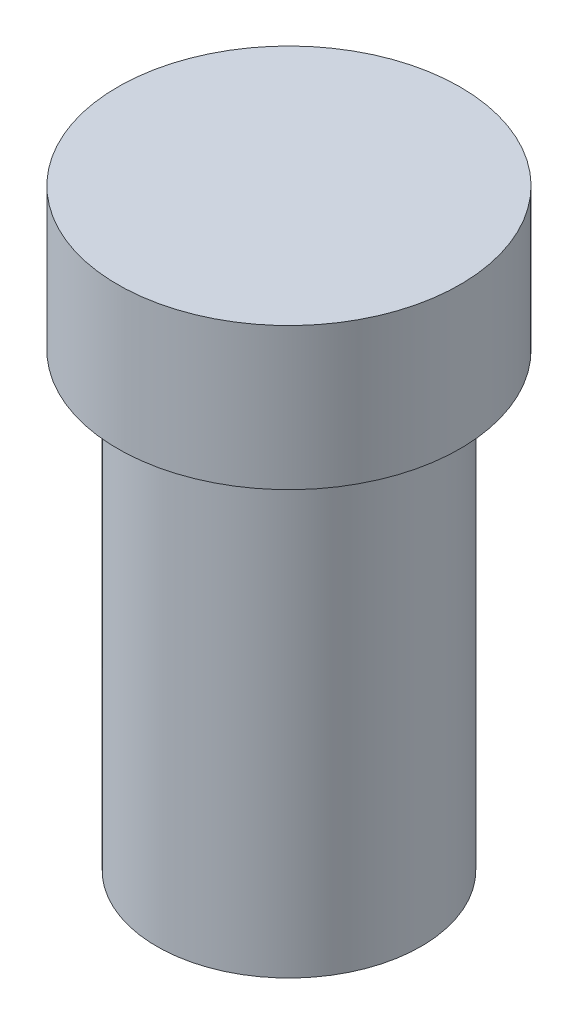
SolidWorks part; units mm, degrees
ref_plane "Front Plane" through (0, 0, 0) normal (0, 0, 1) x (1, 0, 0)
ref_plane "Top Plane" through (0, 0, 0) normal (0, 1, 0) x (1, 0, 0)
ref_plane "Right Plane" through (0, 0, 0) normal (1, 0, 0) x (0, 0, -1)
sketch "Sketch1" plane through (0, 0, 0) normal (0, 0, 1) x (1, 0, 0)
  line L0 (0, 0) -> (0, 102.918) construction
  line L1 (0, 0) -> (22, 0)
  line L2 (22, 0) -> (22, 75)
  line L3 (22, 75) -> (28.5, 75)
  line L4 (28.5, 75) -> (28.5, 98.6593)
  line L5 (28.5, 98.6593) -> (0, 98.6593)
  line L6 (0, 0) -> (0, 98.6593)
  dimension "D1" = 75
  dimension "D2" = 44
  dimension "D3" = 57
revolve "Revolve1" add sketch "Sketch1" angle 360 about L0
fillet "Fillet1" radius 4 1 edges at (0, 75, -22)
